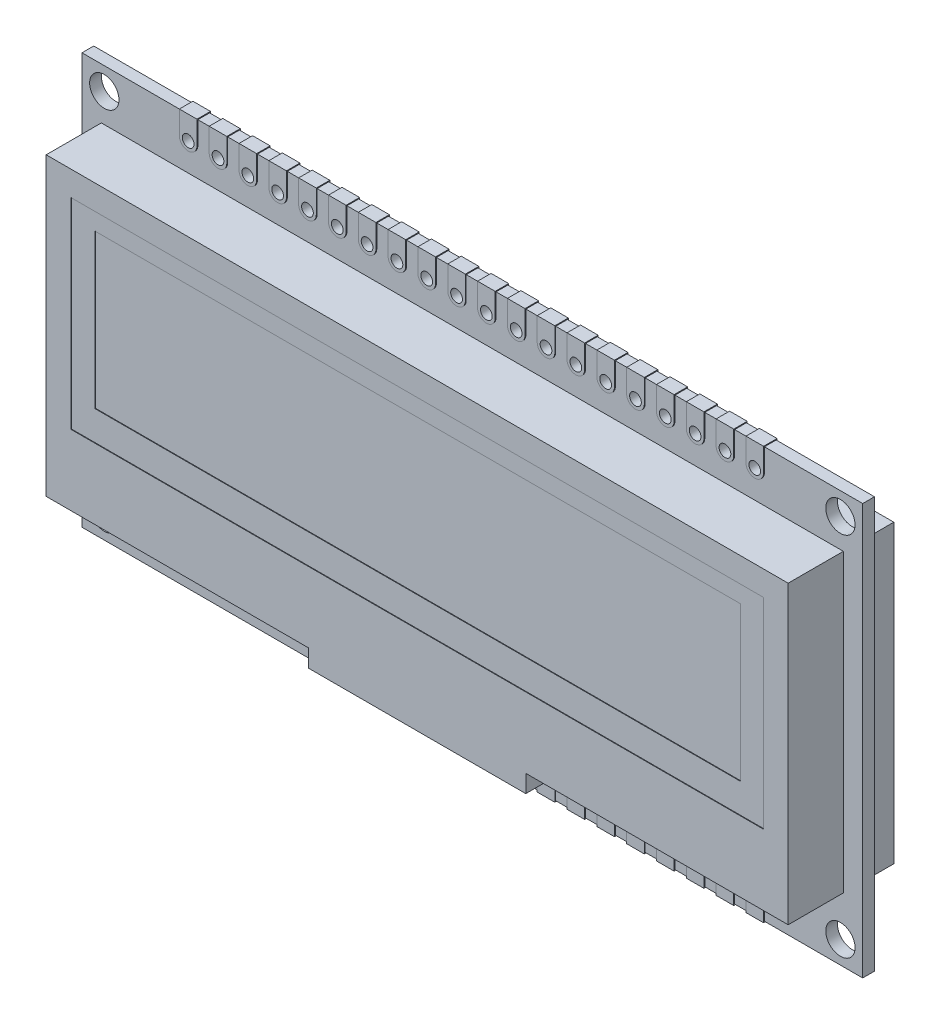
SolidWorks part; units mm, degrees
ref_plane "Front Plane" through (0, 0, 0) normal (0, 0, 1) x (1, 0, 0)
ref_plane "Top Plane" through (0, 0, 0) normal (0, 1, 0) x (1, 0, 0)
ref_plane "Right Plane" through (0, 0, 0) normal (1, 0, 0) x (0, 0, -1)
sketch "Sketch1" plane through (0, 0, 0) normal (0, 0, 1) x (1, 0, 0)
  line L1 (33.25, -17.5) -> (-33.25, -17.5)
  line L2 (33.25, -17.5) -> (33.25, 17.5)
  line L3 (33.25, 17.5) -> (-33.25, 17.5)
  line L4 (-33.25, -17.5) -> (-33.25, 17.5)
  line L5 (33.25, -17.5) -> (-33.25, 17.5) construction
  line L6 (33.25, 17.5) -> (-33.25, -17.5) construction
  circle A0 centre (-31.35, 15.6) radius 1.25
  circle A1 centre (-31.35, -15.6) radius 1.25
  circle A2 centre (31.35, 15.6) radius 1.25
  circle A3 centre (31.35, -15.6) radius 1.25
  point P0 (0, 0)
  point P14 (0, 0)
  point P15 (0, 0)
  point P16 (0, 0)
  dimension "D3" = 2.5
  dimension "D1" = 66.5
  dimension "D2" = 35
  dimension "D4" = 1.9
  dimension "D5" = 1.9
  dimension "D6" = 31.2
  dimension "D7" = 62.7
extrude "Boss-Extrude1" add sketch "Sketch1" along normal mid plane 1
sketch "Sketch3" plane through (0, 0, 0.5) normal (0, 0, 1) x (1, 0, 0)
  line L0 (-24.13, 15.6) -> (-21.59, 15.6) construction
  line L1 (24.13, -15.6) -> (21.59, -15.6) construction
  circle A0 centre (-24.13, 15.6) radius 0.5
  circle A1 centre (-21.59, 15.6) radius 0.5
  circle A2 centre (-19.05, 15.6) radius 0.5
  circle A3 centre (-16.51, 15.6) radius 0.5
  circle A4 centre (-13.97, 15.6) radius 0.5
  circle A5 centre (-11.43, 15.6) radius 0.5
  circle A6 centre (-8.89, 15.6) radius 0.5
  circle A7 centre (-6.35, 15.6) radius 0.5
  circle A8 centre (-3.81, 15.6) radius 0.5
  circle A9 centre (-1.27, 15.6) radius 0.5
  circle A10 centre (1.27, 15.6) radius 0.5
  circle A11 centre (3.81, 15.6) radius 0.5
  circle A12 centre (6.35, 15.6) radius 0.5
  circle A13 centre (8.89, 15.6) radius 0.5
  circle A14 centre (11.43, 15.6) radius 0.5
  circle A15 centre (13.97, 15.6) radius 0.5
  circle A16 centre (16.51, 15.6) radius 0.5
  circle A17 centre (19.05, 15.6) radius 0.5
  circle A18 centre (21.59, 15.6) radius 0.5
  circle A19 centre (24.13, 15.6) radius 0.5
  circle A20 centre (24.13, -15.6) radius 0.5
  circle A21 centre (21.59, -15.6) radius 0.5
  circle A22 centre (19.05, -15.6) radius 0.5
  circle A23 centre (16.51, -15.6) radius 0.5
  circle A24 centre (13.97, -15.6) radius 0.5
  circle A25 centre (11.43, -15.6) radius 0.5
  circle A26 centre (8.89, -15.6) radius 0.5
  circle A27 centre (6.35, -15.6) radius 0.5
  point P3 (31.35, 15.6)
  point P6 (31.35, -15.6)
  dimension "D1" = 1
  dimension "D2" = 7.22
  dimension "D4" = 2.54
  dimension "D6" = 2.54
  dimension "D3" = 20
  dimension "D5" = 8
extrude "Cut-Extrude1" cut sketch "Sketch3" against normal up to next (1 mm away)
sketch "Sketch4" plane through (0, 0, 0) normal (0, 0, 1) x (1, 0, 0)
  line L0 (33.25, 17.5) -> (-33.25, 17.5) construction
  line L2 (-24.88, 15.6) -> (-24.88, 17.575)
  line L3 (-24.88, 17.575) -> (-23.38, 17.575)
  line L4 (-23.38, 15.6) -> (-23.38, 17.575)
  line L5 (-22.34, 15.6) -> (-22.34, 17.575)
  line L6 (-22.34, 17.575) -> (-20.84, 17.575)
  line L7 (-20.84, 15.6) -> (-20.84, 17.575)
  line L8 (-19.8, 15.6) -> (-19.8, 17.575)
  line L9 (-19.8, 17.575) -> (-18.3, 17.575)
  line L10 (-18.3, 15.6) -> (-18.3, 17.575)
  line L11 (-17.26, 15.6) -> (-17.26, 17.575)
  line L12 (-17.26, 17.575) -> (-15.76, 17.575)
  line L13 (-15.76, 15.6) -> (-15.76, 17.575)
  line L14 (-14.72, 15.6) -> (-14.72, 17.575)
  line L15 (-14.72, 17.575) -> (-13.22, 17.575)
  line L16 (-13.22, 15.6) -> (-13.22, 17.575)
  line L17 (-12.18, 15.6) -> (-12.18, 17.575)
  line L18 (-12.18, 17.575) -> (-10.68, 17.575)
  line L19 (-10.68, 15.6) -> (-10.68, 17.575)
  line L20 (-9.64, 15.6) -> (-9.64, 17.575)
  line L21 (-9.64, 17.575) -> (-8.14, 17.575)
  line L22 (-8.14, 15.6) -> (-8.14, 17.575)
  line L23 (-7.1, 15.6) -> (-7.1, 17.575)
  line L24 (-7.1, 17.575) -> (-5.6, 17.575)
  line L25 (-5.6, 15.6) -> (-5.6, 17.575)
  line L26 (-4.56, 15.6) -> (-4.56, 17.575)
  line L27 (-4.56, 17.575) -> (-3.06, 17.575)
  line L28 (-3.06, 15.6) -> (-3.06, 17.575)
  line L29 (-2.02, 15.6) -> (-2.02, 17.575)
  line L30 (-2.02, 17.575) -> (-0.52, 17.575)
  line L31 (-0.52, 15.6) -> (-0.52, 17.575)
  line L32 (0.52, 15.6) -> (0.52, 17.575)
  line L33 (0.52, 17.575) -> (2.02, 17.575)
  line L34 (2.02, 15.6) -> (2.02, 17.575)
  line L35 (3.06, 15.6) -> (3.06, 17.575)
  line L36 (3.06, 17.575) -> (4.56, 17.575)
  line L37 (4.56, 15.6) -> (4.56, 17.575)
  line L38 (5.6, 15.6) -> (5.6, 17.575)
  line L39 (5.6, 17.575) -> (7.1, 17.575)
  line L40 (7.1, 15.6) -> (7.1, 17.575)
  line L41 (8.14, 15.6) -> (8.14, 17.575)
  line L42 (8.14, 17.575) -> (9.64, 17.575)
  line L43 (9.64, 15.6) -> (9.64, 17.575)
  line L44 (10.68, 15.6) -> (10.68, 17.575)
  line L45 (10.68, 17.575) -> (12.18, 17.575)
  line L46 (12.18, 15.6) -> (12.18, 17.575)
  line L47 (13.22, 15.6) -> (13.22, 17.575)
  line L48 (13.22, 17.575) -> (14.72, 17.575)
  line L49 (14.72, 15.6) -> (14.72, 17.575)
  line L50 (15.76, 15.6) -> (15.76, 17.575)
  line L51 (15.76, 17.575) -> (17.26, 17.575)
  line L52 (17.26, 15.6) -> (17.26, 17.575)
  line L53 (18.3, 15.6) -> (18.3, 17.575)
  line L54 (18.3, 17.575) -> (19.8, 17.575)
  line L55 (19.8, 15.6) -> (19.8, 17.575)
  line L56 (20.84, 15.6) -> (20.84, 17.575)
  line L57 (20.84, 17.575) -> (22.34, 17.575)
  line L58 (22.34, 15.6) -> (22.34, 17.575)
  line L59 (23.38, 15.6) -> (23.38, 17.575)
  line L60 (23.38, 17.575) -> (24.88, 17.575)
  line L61 (24.88, 15.6) -> (24.88, 17.575)
  line L62 (-24.88, 15.6) -> (-22.34, 15.6) construction
  line L63 (0, 0) -> (33.25, 0) construction
  line L64 (33.25, -17.5) -> (33.25, 17.5) construction
  line L65 (24.88, -15.6) -> (24.88, -17.575)
  line L66 (23.38, -17.575) -> (24.88, -17.575)
  line L67 (23.38, -15.6) -> (23.38, -17.575)
  line L68 (22.34, -15.6) -> (22.34, -17.575)
  line L69 (20.84, -17.575) -> (22.34, -17.575)
  line L70 (20.84, -15.6) -> (20.84, -17.575)
  line L71 (19.8, -15.6) -> (19.8, -17.575)
  line L72 (18.3, -17.575) -> (19.8, -17.575)
  line L73 (18.3, -15.6) -> (18.3, -17.575)
  line L74 (17.26, -15.6) -> (17.26, -17.575)
  line L75 (15.76, -17.575) -> (17.26, -17.575)
  line L76 (15.76, -15.6) -> (15.76, -17.575)
  line L77 (14.72, -15.6) -> (14.72, -17.575)
  line L78 (13.22, -17.575) -> (14.72, -17.575)
  line L79 (13.22, -15.6) -> (13.22, -17.575)
  line L80 (12.18, -15.6) -> (12.18, -17.575)
  line L81 (10.68, -17.575) -> (12.18, -17.575)
  line L82 (10.68, -15.6) -> (10.68, -17.575)
  line L83 (9.64, -15.6) -> (9.64, -17.575)
  line L84 (8.14, -17.575) -> (9.64, -17.575)
  line L85 (8.14, -15.6) -> (8.14, -17.575)
  line L86 (7.1, -15.6) -> (7.1, -17.575)
  line L87 (5.6, -17.575) -> (7.1, -17.575)
  line L88 (5.6, -15.6) -> (5.6, -17.575)
  arc A0 (-24.88, 15.6) -> (-23.38, 15.6) centre (-24.13, 15.6) ccw
  circle A1 centre (-24.13, 15.6) radius 0.5 construction
  circle A2 centre (-24.13, 15.6) radius 0.5
  arc A3 (-22.34, 15.6) -> (-20.84, 15.6) centre (-21.59, 15.6) ccw
  circle A4 centre (-21.59, 15.6) radius 0.5
  arc A5 (-19.8, 15.6) -> (-18.3, 15.6) centre (-19.05, 15.6) ccw
  circle A6 centre (-19.05, 15.6) radius 0.5
  arc A7 (-17.26, 15.6) -> (-15.76, 15.6) centre (-16.51, 15.6) ccw
  circle A8 centre (-16.51, 15.6) radius 0.5
  arc A9 (-14.72, 15.6) -> (-13.22, 15.6) centre (-13.97, 15.6) ccw
  circle A10 centre (-13.97, 15.6) radius 0.5
  arc A11 (-12.18, 15.6) -> (-10.68, 15.6) centre (-11.43, 15.6) ccw
  circle A12 centre (-11.43, 15.6) radius 0.5
  arc A13 (-9.64, 15.6) -> (-8.14, 15.6) centre (-8.89, 15.6) ccw
  circle A14 centre (-8.89, 15.6) radius 0.5
  arc A15 (-7.1, 15.6) -> (-5.6, 15.6) centre (-6.35, 15.6) ccw
  circle A16 centre (-6.35, 15.6) radius 0.5
  arc A17 (-4.56, 15.6) -> (-3.06, 15.6) centre (-3.81, 15.6) ccw
  circle A18 centre (-3.81, 15.6) radius 0.5
  arc A19 (-2.02, 15.6) -> (-0.52, 15.6) centre (-1.27, 15.6) ccw
  circle A20 centre (-1.27, 15.6) radius 0.5
  arc A21 (0.52, 15.6) -> (2.02, 15.6) centre (1.27, 15.6) ccw
  circle A22 centre (1.27, 15.6) radius 0.5
  arc A23 (3.06, 15.6) -> (4.56, 15.6) centre (3.81, 15.6) ccw
  circle A24 centre (3.81, 15.6) radius 0.5
  arc A25 (5.6, 15.6) -> (7.1, 15.6) centre (6.35, 15.6) ccw
  circle A26 centre (6.35, 15.6) radius 0.5
  arc A27 (8.14, 15.6) -> (9.64, 15.6) centre (8.89, 15.6) ccw
  circle A28 centre (8.89, 15.6) radius 0.5
  arc A29 (10.68, 15.6) -> (12.18, 15.6) centre (11.43, 15.6) ccw
  circle A30 centre (11.43, 15.6) radius 0.5
  arc A31 (13.22, 15.6) -> (14.72, 15.6) centre (13.97, 15.6) ccw
  circle A32 centre (13.97, 15.6) radius 0.5
  arc A33 (15.76, 15.6) -> (17.26, 15.6) centre (16.51, 15.6) ccw
  circle A34 centre (16.51, 15.6) radius 0.5
  arc A35 (18.3, 15.6) -> (19.8, 15.6) centre (19.05, 15.6) ccw
  circle A36 centre (19.05, 15.6) radius 0.5
  arc A37 (20.84, 15.6) -> (22.34, 15.6) centre (21.59, 15.6) ccw
  circle A38 centre (21.59, 15.6) radius 0.5
  arc A39 (23.38, 15.6) -> (24.88, 15.6) centre (24.13, 15.6) ccw
  circle A40 centre (24.13, 15.6) radius 0.5
  circle A41 centre (24.13, -15.6) radius 0.5
  arc A42 (23.38, -15.6) -> (24.88, -15.6) centre (24.13, -15.6) cw
  circle A43 centre (21.59, -15.6) radius 0.5
  arc A44 (20.84, -15.6) -> (22.34, -15.6) centre (21.59, -15.6) cw
  circle A45 centre (19.05, -15.6) radius 0.5
  arc A46 (18.3, -15.6) -> (19.8, -15.6) centre (19.05, -15.6) cw
  circle A47 centre (16.51, -15.6) radius 0.5
  arc A48 (15.76, -15.6) -> (17.26, -15.6) centre (16.51, -15.6) cw
  circle A49 centre (13.97, -15.6) radius 0.5
  arc A50 (13.22, -15.6) -> (14.72, -15.6) centre (13.97, -15.6) cw
  circle A51 centre (11.43, -15.6) radius 0.5
  arc A52 (10.68, -15.6) -> (12.18, -15.6) centre (11.43, -15.6) cw
  circle A53 centre (8.89, -15.6) radius 0.5
  arc A54 (8.14, -15.6) -> (9.64, -15.6) centre (8.89, -15.6) cw
  circle A55 centre (6.35, -15.6) radius 0.5
  arc A56 (5.6, -15.6) -> (7.1, -15.6) centre (6.35, -15.6) cw
  dimension "D1" = 1.5
  dimension "D2" = 0.075
  dimension "D4" = 2.54
  dimension "D3" = 20
extrude "Boss-Extrude3" add sketch "Sketch4" along normal mid plane 1.15
sketch "Sketch2" plane through (0, 0, 0.5) normal (0, 0, 1) x (1, 0, 0)
  line L0 (33.25, 17.5) -> (24.88, 17.5) construction
  line L1 (-31.6, 13.15) -> (31.6, 13.15)
  line L2 (-31.6, 13.15) -> (-31.6, -12.05)
  line L3 (-31.6, -12.05) -> (-9.25, -12.05)
  line L4 (31.6, 13.15) -> (31.6, -12.05)
  line L5 (-33.25, 17.5) -> (-33.25, -17.5) construction
  line L6 (9.25, -12.05) -> (31.6, -12.05)
  line L7 (9.25, -13.55) -> (-9.25, -13.55)
  line L8 (9.25, -13.55) -> (9.25, -12.05)
  line L10 (-9.25, -13.55) -> (-9.25, -12.05)
  line L11 (9.25, -13.55) -> (-9.25, -12.05) construction
  line L12 (9.25, -12.05) -> (-9.25, -13.55) construction
  point P8 (0, -12.8)
  point P13 (0, 0)
  point P15 (0, 0)
  point P16 (0, 0)
  point P17 (0, 0)
  dimension "D1" = 4.35
  dimension "D2" = 25.2
  dimension "D3" = 1.65
  dimension "D4" = 63.2
  dimension "D5" = 1.5
  dimension "D6" = 18.5
extrude "Boss-Extrude2" add sketch "Sketch2" along normal blind 4.7 separate body
sketch "Sketch5" plane through (0, 0, 5.2) normal (0, 0, 1) x (1, 0, 0)
  line L0 (-24.88, 17.5) -> (-33.25, 17.5) construction
  line L1 (-29.5, 11.05) -> (29.5, 11.05)
  line L2 (-29.5, 11.05) -> (-29.5, -6.05)
  line L3 (-29.5, -6.05) -> (29.5, -6.05)
  line L4 (29.5, 11.05) -> (29.5, -6.05)
  line L5 (-33.25, 17.5) -> (-33.25, -17.5) construction
  dimension "D1" = 6.45
  dimension "D2" = 17.1
  dimension "D3" = 3.75
  dimension "D4" = 59
extrude "Cut-Extrude2" cut sketch "Sketch5" against normal blind 0.05
sketch "Sketch6" plane through (0, 0, 5.15) normal (0, 0, 1) x (1, 0, 0)
  line L0 (-33.25, 17.5) -> (-33.25, -17.5) construction
  line L1 (-27.51, 9.55) -> (27.508, 9.55)
  line L2 (-27.51, 9.55) -> (-27.51, -3.548)
  line L3 (-27.51, -3.548) -> (27.508, -3.548)
  line L4 (27.508, 9.55) -> (27.508, -3.548)
  line L5 (-24.88, 17.5) -> (-33.25, 17.5) construction
  dimension "D1" = 5.74
  dimension "D2" = 55.018
  dimension "D3" = 7.95
  dimension "D4" = 13.098
extrude "Cut-Extrude3" cut sketch "Sketch6" against normal blind 0.05
sketch "Sketch7" plane through (0, 0, -0.5) normal (0, 0, -1) x (-1, 0, 0)
  line L0 (-31.6, 13.15) -> (31.6, 13.15) construction
  line L1 (-31.6, 13.15) -> (31.6, 13.15)
  line L2 (-31.6, 13.15) -> (-31.6, -12.05)
  line L3 (-31.6, -12.05) -> (31.6, -12.05)
  line L4 (31.6, 13.15) -> (31.6, -12.05)
  line L5 (-9.25, -12.05) -> (-31.6, -12.05) construction
  line L6 (-31.6, -12.05) -> (-31.6, 13.15) construction
  line L7 (31.6, 13.15) -> (31.6, -12.05) construction
extrude "Boss-Extrude4" add sketch "Sketch7" along normal blind 3.3
sketch "Sketch8" plane through (0, 0, -3.8) normal (0, 0, -1) x (-1, 0, 0)
  line L0 (-31.6, -1.3776) -> (31.6, -1.3776) construction
  line L1 (-31.6, 13.15) -> (-31.6, -12.05) construction
  line L2 (31.6, -12.05) -> (31.6, 13.15) construction
  text T0 "<b>KEEP OUT ZONE</b>"
extrude "Cut-Extrude4" cut sketch "Sketch8" against normal blind 0.05
